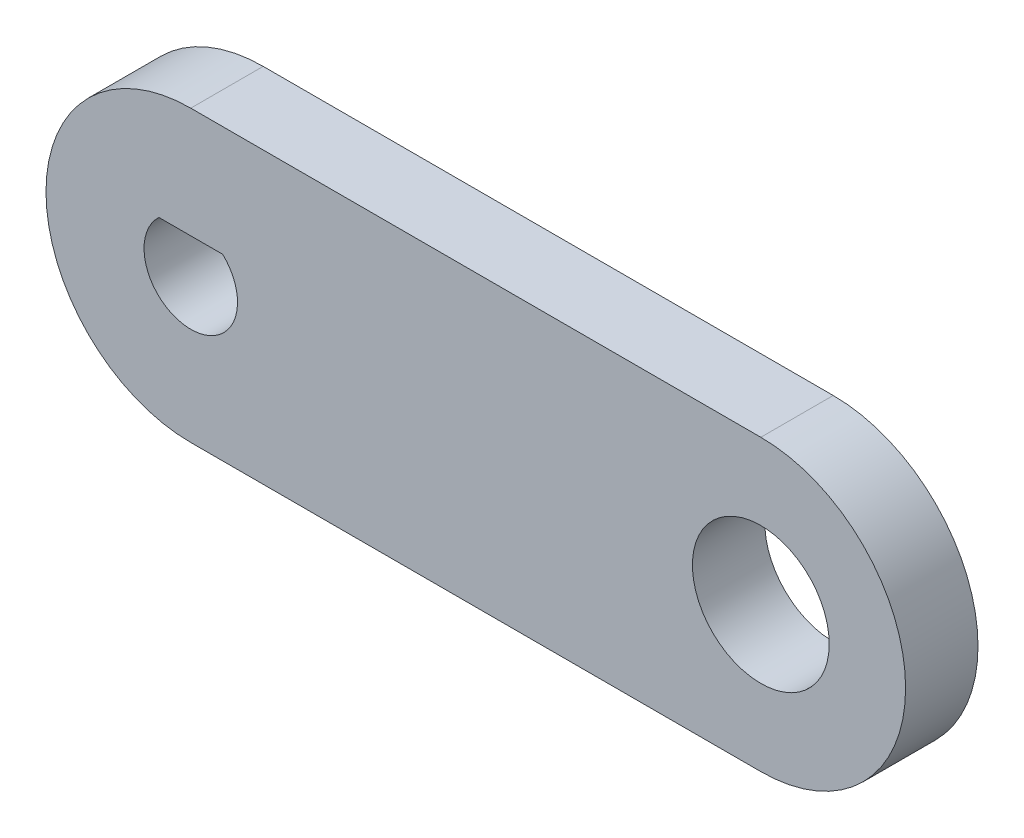
SolidWorks part; units mm, degrees
ref_plane "Front Plane" through (0, 0, 0) normal (0, 0, 1) x (1, 0, 0)
ref_plane "Top Plane" through (0, 0, 0) normal (0, 1, 0) x (1, 0, 0)
ref_plane "Right Plane" through (0, 0, 0) normal (1, 0, 0) x (0, 0, -1)
sketch "Sketch1" plane through (0, 0, 0) normal (0, 0, 1) x (1, 0, 0)
  line L0 (25, 6.35) -> (0, 6.35)
  line L1 (0, -6.35) -> (25, -6.35)
  line L2 (-1.3973, 1.5) -> (1.3973, 1.5)
  arc A0 (-1.3973, 1.5) -> (1.3973, 1.5) centre (0, 0) ccw
  circle A1 centre (25, 0) radius 3
  arc A2 (0, 6.35) -> (0, -6.35) centre (0, 0) ccw
  arc A3 (25, -6.35) -> (25, 6.35) centre (25, 0) ccw
  dimension "D1" = 4.1
  dimension "D2" = 1.5
  dimension "D5" = 6
  dimension "D3" = 12.7
  dimension "D4" = 25
extrude "Extrude1" add sketch "Sketch1" against normal blind 3.175
